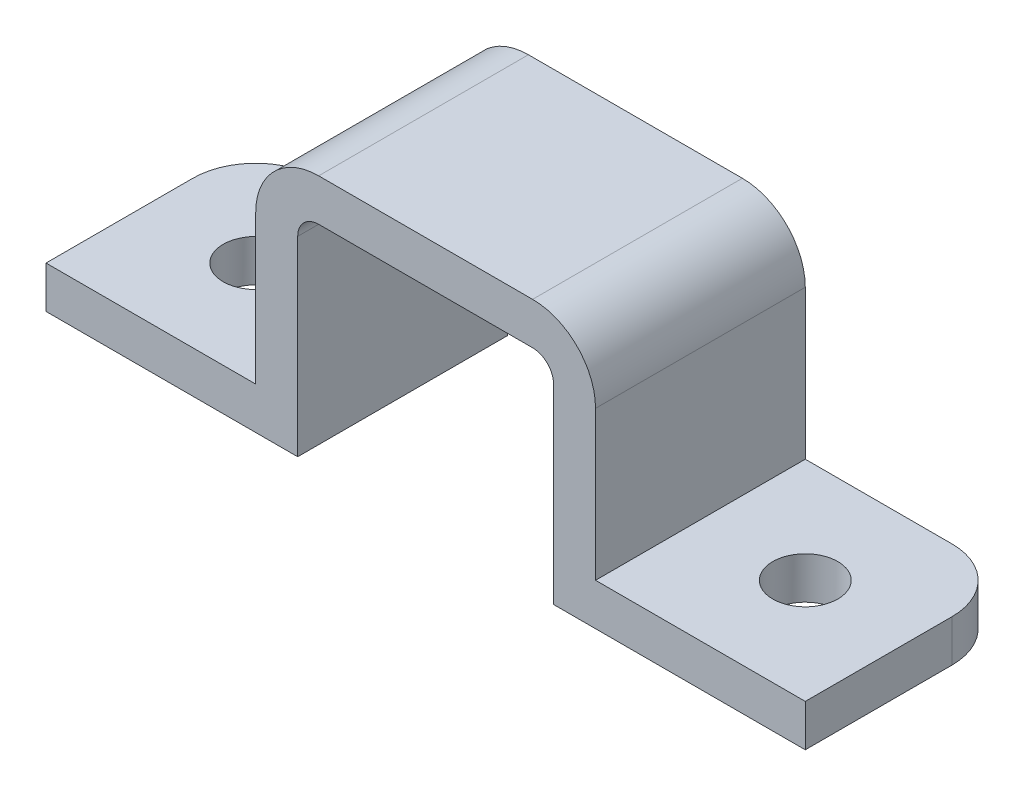
SolidWorks part; units mm, degrees
ref_plane "Front Plane" through (0, 0, 0) normal (0, 0, 1) x (1, 0, 0)
ref_plane "Top Plane" through (0, 0, 0) normal (0, 1, 0) x (1, 0, 0)
ref_plane "Right Plane" through (0, 0, 0) normal (1, 0, 0) x (0, 0, -1)
sketch "Sketch1" plane through (0, 0, 0) normal (0, 0, 1) x (1, 0, 0)
  line L0 (0, 18.5517) -> (0, -17.7555) construction
  line L1 (-25.7972, 0) -> (26.5934, 0) construction
  line L2 (6.1, 10.1) -> (-6.1, 10.1)
  line L3 (-6.1, 10.1) -> (-6.1, 0)
  line L4 (-6.1, 0) -> (-18.1, 0)
  line L5 (-18.1, 0) -> (-18.1, 2)
  line L6 (-18.1, 2) -> (-8.1, 2)
  line L7 (-8.1, 2) -> (-8.1, 12.1)
  line L8 (-8.1, 12.1) -> (8.1, 12.1)
  line L9 (18.1, 0) -> (18.1, 2)
  line L10 (25.7972, 0) -> (-26.5934, 0) construction
  line L11 (8.1, 2) -> (8.1, 12.1)
  line L12 (18.1, 2) -> (8.1, 2)
  line L13 (6.1, 0) -> (18.1, 0)
  line L14 (6.1, 10.1) -> (6.1, 0)
  point P18 (0, 12.1)
  point P21 (0, 10.1)
  dimension "D1" = 2
  dimension "D2" = 2
  dimension "D3" = 10.1
  dimension "D4" = 12
  dimension "D5" = 6.1
  dimension "D6" = 2
extrude "Boss-Extrude1" add sketch "Sketch1" along normal blind 10
sketch "Sketch2" plane through (0, 2, 0) normal (0, 1, 0) x (1, 0, 0)
  line L0 (-18.1, 0) -> (-8.1, -10) construction
  line L1 (-8.1, 0) -> (-18.1, -10) construction
  circle A0 centre (-13.1, -5) radius 1.55
  dimension "D1" = 3.1
extrude "Cut-Extrude1" cut sketch "Sketch2" against normal blind 10
sketch "Sketch3" plane through (0, 2, 0) normal (0, 1, 0) x (1, 0, 0)
  line L0 (8.1, -10) -> (18.1, 0) construction
  line L1 (18.1, -10) -> (8.5, 0) construction
  line L2 (18.1, 0) -> (8.1, 0) construction
  circle A0 centre (13.1, -5) radius 1.55
  dimension "D1" = 3.1
extrude "Cut-Extrude2" cut sketch "Sketch3" against normal blind 10
fillet "Fillet1" radius 3 2 edges at (18.1, 1, 0) (-18.1, 1, 0)
fillet "Fillet2" radius 3 2 edges at (8.1, 12.1, 5) (-8.1, 12.1, 5)
fillet "Fillet3" radius 1 2 edges at (6.1, 10.1, 5) (-6.1, 10.1, 5)
